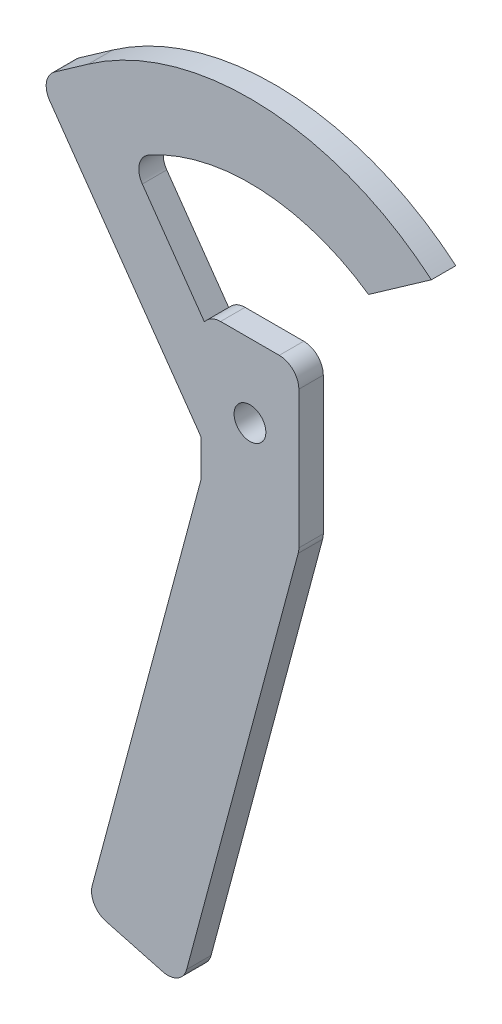
SolidWorks part; units mm, degrees
ref_plane "Front Plane" through (0, 0, 0) normal (0, 0, 1) x (1, 0, 0)
ref_plane "Top Plane" through (0, 0, 0) normal (0, 1, 0) x (1, 0, 0)
ref_plane "Right Plane" through (0, 0, 0) normal (1, 0, 0) x (0, 0, -1)
sketch "Model" plane through (0, 0, 0) normal (0, 0, 1) x (1, 0, 0)
  line L113 (260.4811, 253.3785) -> (253.5582, 248.516)
  line L114 (317.7843, 241.2253) -> (330.6351, 250.2515)
  line L115 (282.7595, 199.9822) -> (283.5081, 198.8554)
  line L116 (283.5081, 198.8554) -> (283.5305, 198.8255)
  line L117 (284.2236, 219.5759) -> (271.5215, 237.6601)
  line L118 (252.584, 242.9437) -> (282.7595, 199.9822)
  line L119 (303.5305, 189.219) -> (303.5305, 217.3255)
  line L120 (283.3942, 190.8168) -> (261.272, 108.2559)
  line L121 (283.5305, 217.3255) -> (283.5305, 191.8521)
  line L122 (299.5305, 221.3255) -> (287.5305, 221.3255)
  line L123 (280.5905, 103.0795) -> (303.3942, 188.1838)
  line L124 (264.1004, 103.3569) -> (275.6916, 100.2511)
  arc A0 (317.7843, 241.2253) -> (272.8482, 243.4536) centre (293.5305, 206.3255) ccw
  arc A1 (272.8482, 243.4536) -> (271.5215, 237.6601) centre (274.7948, 239.9592) ccw
  arc A2 (330.6351, 250.2515) -> (260.4811, 253.3785) centre (293.5305, 206.3255) ccw
  arc A3 (303.5305, 198.8255) -> (303.5305, 213.8255) centre (293.5305, 206.3255) ccw
  arc A4 (253.5582, 248.516) -> (252.584, 242.9437) centre (255.8573, 245.2428) ccw
  arc A5 (303.5305, 217.3255) -> (299.5305, 221.3255) centre (299.5305, 217.3255) ccw
  arc A6 (303.3942, 188.1838) -> (303.5305, 189.219) centre (299.5305, 189.219) ccw
  arc A7 (275.6916, 100.2511) -> (280.5905, 103.0795) centre (276.7268, 104.1148) ccw
  arc A8 (261.272, 108.2559) -> (264.1004, 103.3569) centre (265.1357, 107.2206) ccw
  arc A9 (283.3942, 190.8168) -> (283.5305, 191.8521) centre (279.5305, 191.8521) ccw
  arc A10 (287.5305, 221.3255) -> (283.5305, 217.3255) centre (287.5305, 217.3255) ccw
  circle A11 centre (293.5305, 198.3255) radius 2.075
  circle A12 centre (293.5305, 214.3255) radius 2.075
  circle A13 centre (293.5305, 206.3255) radius 3.25
extrude "Boss-Extrude1" add sketch "Model" along normal blind 5 contours L122 A10 L121 A9 L120 A8 L124 A7 L123 A6 L119 A5 A13 A12 A11 | A10 L117 A1 A0 L114 A2 L113 A4 L118 L115 L116 L121 | A11 | A12
